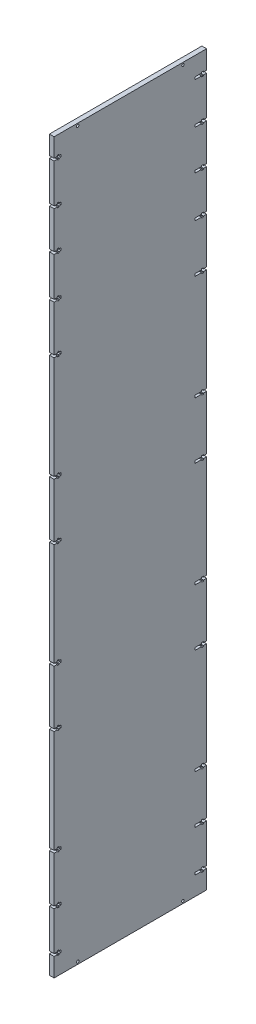
SolidWorks part; units mm, degrees
material "Acrylic (Medium-high impact)"
ref_plane "Front Plane" through (0, 0, 0) normal (0, 0, 1) x (1, 0, 0)
ref_plane "Top Plane" through (0, 0, 0) normal (0, 1, 0) x (1, 0, 0)
ref_plane "Right Plane" through (0, 0, 0) normal (1, 0, 0) x (0, 0, -1)
sketch "Sketch1" plane through (0, 0, 0) normal (1, 0, 0) x (0, 0, -1)
  line L0 (0, 100) -> (188.4, 100) construction
  line L1 (0, 0) -> (188.4, 0)
  line L2 (0, 0) -> (0, 900)
  line L3 (0, 900) -> (188.4, 900)
  line L4 (188.4, 0) -> (188.4, 900)
  line L5 (94.2, 900) -> (94.2, 0) construction
  line L6 (0, 450) -> (188.4, 450) construction
  line L7 (0, 300) -> (188.4, 300) construction
  line L8 (0, 500) -> (188.4, 500) construction
  line L9 (0, 700) -> (188.4, 700) construction
  line L10 (0, 800) -> (188.4, 800) construction
  line L11 (0, 850) -> (188.4, 850) construction
  line L12 (0, 750) -> (188.4, 750) construction
  line L13 (0, 600) -> (188.4, 600) construction
  line L14 (0, 400) -> (188.4, 400) construction
  line L15 (0, 200) -> (188.4, 200) construction
  line L16 (0, 50) -> (188.4, 50) construction
  line L29 (6.35, 877) -> (6.35, 878.21)
  line L30 (8.35, 874) -> (8.35, 877)
  line L31 (6.35, 877) -> (8.35, 877)
  line L32 (6.35, 874) -> (8.35, 874)
  line L33 (6.35, 872.79) -> (6.35, 874)
  line L34 (4, 878.21) -> (6.35, 878.21)
  line L35 (4, 872.79) -> (4, 874)
  line L36 (4, 872.79) -> (6.35, 872.79)
  line L37 (4, 877) -> (4, 878.21)
  line L38 (0, 877) -> (4, 877)
  line L39 (0, 874) -> (0, 877)
  line L40 (0, 874) -> (4, 874)
  line L41 (0, 826) -> (4, 826)
  line L42 (0, 826) -> (0, 823)
  line L43 (0, 823) -> (4, 823)
  line L44 (4, 823) -> (4, 821.79)
  line L45 (4, 827.21) -> (6.35, 827.21)
  line L46 (4, 827.21) -> (4, 826)
  line L47 (4, 821.79) -> (6.35, 821.79)
  line L48 (6.35, 827.21) -> (6.35, 826)
  line L49 (6.35, 826) -> (8.35, 826)
  line L50 (6.35, 823) -> (8.35, 823)
  line L51 (8.35, 826) -> (8.35, 823)
  line L52 (6.35, 823) -> (6.35, 821.79)
  line L53 (6.35, 777) -> (6.35, 778.21)
  line L54 (8.35, 774) -> (8.35, 777)
  line L55 (6.35, 777) -> (8.35, 777)
  line L56 (6.35, 774) -> (8.35, 774)
  line L57 (6.35, 772.79) -> (6.35, 774)
  line L58 (4, 778.21) -> (6.35, 778.21)
  line L59 (4, 772.79) -> (4, 774)
  line L60 (4, 772.79) -> (6.35, 772.79)
  line L61 (4, 777) -> (4, 778.21)
  line L62 (0, 777) -> (4, 777)
  line L63 (0, 774) -> (0, 777)
  line L64 (0, 774) -> (4, 774)
  line L65 (0, 726) -> (4, 726)
  line L66 (0, 726) -> (0, 723)
  line L67 (0, 723) -> (4, 723)
  line L68 (4, 723) -> (4, 721.79)
  line L69 (4, 727.21) -> (6.35, 727.21)
  line L70 (4, 727.21) -> (4, 726)
  line L71 (4, 721.79) -> (6.35, 721.79)
  line L72 (6.35, 727.21) -> (6.35, 726)
  line L73 (6.35, 726) -> (8.35, 726)
  line L74 (6.35, 723) -> (8.35, 723)
  line L75 (8.35, 726) -> (8.35, 723)
  line L76 (6.35, 723) -> (6.35, 721.79)
  line L77 (6.35, 666.5) -> (6.35, 667.71)
  line L78 (8.35, 663.5) -> (8.35, 666.5)
  line L79 (6.35, 666.5) -> (8.35, 666.5)
  line L80 (6.35, 663.5) -> (8.35, 663.5)
  line L81 (6.35, 662.29) -> (6.35, 663.5)
  line L82 (4, 667.71) -> (6.35, 667.71)
  line L83 (4, 662.29) -> (4, 663.5)
  line L84 (4, 662.29) -> (6.35, 662.29)
  line L85 (4, 666.5) -> (4, 667.71)
  line L86 (0, 666.5) -> (4, 666.5)
  line L87 (0, 663.5) -> (4, 663.5)
  line L88 (0, 666.5) -> (0, 663.5)
  line L89 (0, 533.5) -> (0, 536.5)
  line L90 (0, 536.5) -> (4, 536.5)
  line L91 (0, 533.5) -> (4, 533.5)
  line L92 (4, 533.5) -> (4, 532.29)
  line L93 (4, 537.71) -> (6.35, 537.71)
  line L94 (4, 537.71) -> (4, 536.5)
  line L95 (4, 532.29) -> (6.35, 532.29)
  line L96 (6.35, 537.71) -> (6.35, 536.5)
  line L97 (6.35, 536.5) -> (8.35, 536.5)
  line L98 (6.35, 533.5) -> (8.35, 533.5)
  line L99 (8.35, 536.5) -> (8.35, 533.5)
  line L100 (6.35, 533.5) -> (6.35, 532.29)
  line L101 (0, 336.5) -> (4, 336.5)
  line L102 (0, 333.5) -> (4, 333.5)
  line L103 (4, 333.5) -> (4, 332.29)
  line L104 (4, 337.71) -> (6.35, 337.71)
  line L105 (4, 337.71) -> (4, 336.5)
  line L106 (4, 332.29) -> (6.35, 332.29)
  line L107 (6.35, 337.71) -> (6.35, 336.5)
  line L108 (6.35, 336.5) -> (8.35, 336.5)
  line L109 (6.35, 333.5) -> (8.35, 333.5)
  line L110 (8.35, 336.5) -> (8.35, 333.5)
  line L111 (6.35, 333.5) -> (6.35, 332.29)
  line L112 (6.35, 466.5) -> (6.35, 467.71)
  line L113 (8.35, 463.5) -> (8.35, 466.5)
  line L114 (6.35, 466.5) -> (8.35, 466.5)
  line L115 (6.35, 463.5) -> (8.35, 463.5)
  line L116 (6.35, 462.29) -> (6.35, 463.5)
  line L117 (4, 467.71) -> (6.35, 467.71)
  line L118 (4, 462.29) -> (4, 463.5)
  line L119 (4, 462.29) -> (6.35, 462.29)
  line L120 (4, 466.5) -> (4, 467.71)
  line L121 (0, 466.5) -> (4, 466.5)
  line L122 (0, 463.5) -> (4, 463.5)
  line L123 (0, 136.5) -> (4, 136.5)
  line L124 (0, 133.5) -> (4, 133.5)
  line L125 (4, 133.5) -> (4, 132.29)
  line L126 (4, 137.71) -> (6.35, 137.71)
  line L127 (4, 137.71) -> (4, 136.5)
  line L128 (4, 132.29) -> (6.35, 132.29)
  line L129 (6.35, 137.71) -> (6.35, 136.5)
  line L130 (6.35, 136.5) -> (8.35, 136.5)
  line L131 (6.35, 133.5) -> (8.35, 133.5)
  line L132 (8.35, 136.5) -> (8.35, 133.5)
  line L133 (6.35, 133.5) -> (6.35, 132.29)
  line L134 (6.35, 266.5) -> (6.35, 267.71)
  line L135 (8.35, 263.5) -> (8.35, 266.5)
  line L136 (6.35, 266.5) -> (8.35, 266.5)
  line L137 (6.35, 263.5) -> (8.35, 263.5)
  line L138 (6.35, 262.29) -> (6.35, 263.5)
  line L139 (4, 267.71) -> (6.35, 267.71)
  line L140 (4, 262.29) -> (4, 263.5)
  line L141 (4, 262.29) -> (6.35, 262.29)
  line L142 (4, 266.5) -> (4, 267.71)
  line L143 (0, 266.5) -> (4, 266.5)
  line L144 (0, 263.5) -> (4, 263.5)
  line L145 (6.35, 77) -> (6.35, 78.21)
  line L146 (8.35, 74) -> (8.35, 77)
  line L147 (6.35, 77) -> (8.35, 77)
  line L148 (6.35, 74) -> (8.35, 74)
  line L149 (6.35, 72.79) -> (6.35, 74)
  line L150 (4, 78.21) -> (6.35, 78.21)
  line L151 (4, 72.79) -> (4, 74)
  line L152 (4, 72.79) -> (6.35, 72.79)
  line L153 (4, 77) -> (4, 78.21)
  line L154 (0, 77) -> (4, 77)
  line L155 (0, 74) -> (4, 74)
  line L156 (0, 26) -> (4, 26)
  line L157 (0, 23) -> (4, 23)
  line L158 (4, 23) -> (4, 21.79)
  line L159 (4, 27.21) -> (6.35, 27.21)
  line L160 (4, 27.21) -> (4, 26)
  line L161 (4, 21.79) -> (6.35, 21.79)
  line L162 (6.35, 27.21) -> (6.35, 26)
  line L163 (6.35, 26) -> (8.35, 26)
  line L164 (6.35, 23) -> (8.35, 23)
  line L165 (8.35, 26) -> (8.35, 23)
  line L166 (6.35, 23) -> (6.35, 21.79)
  line L167 (0, 74) -> (0, 24.2711) construction
  line L168 (188.4, 23) -> (184.4, 23)
  line L169 (188.4, 26) -> (184.4, 26)
  line L170 (182.05, 23) -> (182.05, 21.79)
  line L171 (180.05, 26) -> (180.05, 23)
  line L172 (182.05, 23) -> (180.05, 23)
  line L173 (182.05, 26) -> (180.05, 26)
  line L174 (182.05, 27.21) -> (182.05, 26)
  line L175 (184.4, 21.79) -> (182.05, 21.79)
  line L176 (184.4, 27.21) -> (184.4, 26)
  line L177 (184.4, 27.21) -> (182.05, 27.21)
  line L178 (184.4, 23) -> (184.4, 21.79)
  line L179 (188.4, 74) -> (184.4, 74)
  line L180 (188.4, 77) -> (184.4, 77)
  line L181 (184.4, 77) -> (184.4, 78.21)
  line L182 (184.4, 72.79) -> (182.05, 72.79)
  line L183 (184.4, 72.79) -> (184.4, 74)
  line L184 (184.4, 78.21) -> (182.05, 78.21)
  line L185 (182.05, 72.79) -> (182.05, 74)
  line L186 (182.05, 74) -> (180.05, 74)
  line L187 (182.05, 77) -> (180.05, 77)
  line L188 (180.05, 74) -> (180.05, 77)
  line L189 (182.05, 77) -> (182.05, 78.21)
  line L190 (182.05, 133.5) -> (182.05, 132.29)
  line L191 (180.05, 136.5) -> (180.05, 133.5)
  line L192 (182.05, 133.5) -> (180.05, 133.5)
  line L193 (182.05, 136.5) -> (180.05, 136.5)
  line L194 (182.05, 137.71) -> (182.05, 136.5)
  line L195 (184.4, 132.29) -> (182.05, 132.29)
  line L196 (184.4, 137.71) -> (184.4, 136.5)
  line L197 (184.4, 137.71) -> (182.05, 137.71)
  line L198 (184.4, 133.5) -> (184.4, 132.29)
  line L199 (188.4, 133.5) -> (184.4, 133.5)
  line L200 (188.4, 136.5) -> (184.4, 136.5)
  line L201 (188.4, 263.5) -> (184.4, 263.5)
  line L202 (188.4, 266.5) -> (184.4, 266.5)
  line L203 (184.4, 266.5) -> (184.4, 267.71)
  line L204 (184.4, 262.29) -> (182.05, 262.29)
  line L205 (184.4, 262.29) -> (184.4, 263.5)
  line L206 (184.4, 267.71) -> (182.05, 267.71)
  line L207 (182.05, 262.29) -> (182.05, 263.5)
  line L208 (182.05, 263.5) -> (180.05, 263.5)
  line L209 (182.05, 266.5) -> (180.05, 266.5)
  line L210 (180.05, 263.5) -> (180.05, 266.5)
  line L211 (182.05, 266.5) -> (182.05, 267.71)
  line L212 (182.05, 333.5) -> (182.05, 332.29)
  line L213 (180.05, 336.5) -> (180.05, 333.5)
  line L214 (182.05, 333.5) -> (180.05, 333.5)
  line L215 (182.05, 336.5) -> (180.05, 336.5)
  line L216 (182.05, 337.71) -> (182.05, 336.5)
  line L217 (184.4, 332.29) -> (182.05, 332.29)
  line L218 (184.4, 337.71) -> (184.4, 336.5)
  line L219 (184.4, 337.71) -> (182.05, 337.71)
  line L220 (184.4, 333.5) -> (184.4, 332.29)
  line L221 (188.4, 333.5) -> (184.4, 333.5)
  line L222 (188.4, 336.5) -> (184.4, 336.5)
  line L223 (188.4, 463.5) -> (184.4, 463.5)
  line L224 (188.4, 466.5) -> (184.4, 466.5)
  line L225 (184.4, 466.5) -> (184.4, 467.71)
  line L226 (184.4, 462.29) -> (182.05, 462.29)
  line L227 (184.4, 462.29) -> (184.4, 463.5)
  line L228 (184.4, 467.71) -> (182.05, 467.71)
  line L229 (182.05, 462.29) -> (182.05, 463.5)
  line L230 (182.05, 463.5) -> (180.05, 463.5)
  line L231 (182.05, 466.5) -> (180.05, 466.5)
  line L232 (180.05, 463.5) -> (180.05, 466.5)
  line L233 (182.05, 466.5) -> (182.05, 467.71)
  line L234 (182.05, 533.5) -> (182.05, 532.29)
  line L235 (180.05, 536.5) -> (180.05, 533.5)
  line L236 (182.05, 533.5) -> (180.05, 533.5)
  line L237 (182.05, 536.5) -> (180.05, 536.5)
  line L238 (182.05, 537.71) -> (182.05, 536.5)
  line L239 (184.4, 532.29) -> (182.05, 532.29)
  line L240 (184.4, 537.71) -> (184.4, 536.5)
  line L241 (184.4, 537.71) -> (182.05, 537.71)
  line L242 (184.4, 533.5) -> (184.4, 532.29)
  line L243 (188.4, 533.5) -> (184.4, 533.5)
  line L244 (188.4, 536.5) -> (184.4, 536.5)
  line L245 (188.4, 663.5) -> (184.4, 663.5)
  line L246 (188.4, 666.5) -> (184.4, 666.5)
  line L247 (184.4, 666.5) -> (184.4, 667.71)
  line L248 (184.4, 662.29) -> (182.05, 662.29)
  line L249 (184.4, 662.29) -> (184.4, 663.5)
  line L250 (184.4, 667.71) -> (182.05, 667.71)
  line L251 (182.05, 662.29) -> (182.05, 663.5)
  line L252 (182.05, 663.5) -> (180.05, 663.5)
  line L253 (182.05, 666.5) -> (180.05, 666.5)
  line L254 (180.05, 663.5) -> (180.05, 666.5)
  line L255 (182.05, 666.5) -> (182.05, 667.71)
  line L256 (182.05, 723) -> (182.05, 721.79)
  line L257 (180.05, 726) -> (180.05, 723)
  line L258 (182.05, 723) -> (180.05, 723)
  line L259 (182.05, 726) -> (180.05, 726)
  line L260 (182.05, 727.21) -> (182.05, 726)
  line L261 (184.4, 721.79) -> (182.05, 721.79)
  line L262 (184.4, 727.21) -> (184.4, 726)
  line L263 (184.4, 727.21) -> (182.05, 727.21)
  line L264 (184.4, 723) -> (184.4, 721.79)
  line L265 (188.4, 723) -> (184.4, 723)
  line L266 (188.4, 726) -> (184.4, 726)
  line L267 (188.4, 774) -> (184.4, 774)
  line L268 (188.4, 777) -> (184.4, 777)
  line L269 (184.4, 777) -> (184.4, 778.21)
  line L270 (184.4, 772.79) -> (182.05, 772.79)
  line L271 (184.4, 772.79) -> (184.4, 774)
  line L272 (184.4, 778.21) -> (182.05, 778.21)
  line L273 (182.05, 772.79) -> (182.05, 774)
  line L274 (182.05, 774) -> (180.05, 774)
  line L275 (182.05, 777) -> (180.05, 777)
  line L276 (180.05, 774) -> (180.05, 777)
  line L277 (182.05, 777) -> (182.05, 778.21)
  line L278 (182.05, 823) -> (182.05, 821.79)
  line L279 (180.05, 826) -> (180.05, 823)
  line L280 (182.05, 823) -> (180.05, 823)
  line L281 (182.05, 826) -> (180.05, 826)
  line L282 (182.05, 827.21) -> (182.05, 826)
  line L283 (184.4, 821.79) -> (182.05, 821.79)
  line L284 (184.4, 827.21) -> (184.4, 826)
  line L285 (184.4, 827.21) -> (182.05, 827.21)
  line L286 (184.4, 823) -> (184.4, 821.79)
  line L287 (188.4, 823) -> (184.4, 823)
  line L288 (188.4, 826) -> (184.4, 826)
  line L289 (188.4, 874) -> (184.4, 874)
  line L290 (188.4, 877) -> (184.4, 877)
  line L291 (184.4, 877) -> (184.4, 878.21)
  line L292 (184.4, 872.79) -> (182.05, 872.79)
  line L293 (184.4, 872.79) -> (184.4, 874)
  line L294 (184.4, 878.21) -> (182.05, 878.21)
  line L295 (182.05, 872.79) -> (182.05, 874)
  line L296 (182.05, 874) -> (180.05, 874)
  line L297 (182.05, 877) -> (180.05, 877)
  line L298 (180.05, 874) -> (180.05, 877)
  line L299 (182.05, 877) -> (182.05, 878.21)
  line L301 (12.141, 850) -> (0, 850) construction
  line L317 (12.141, 750) -> (0, 750) construction
  line L323 (12.141, 600) -> (0, 600) construction
  line L329 (12.141, 50) -> (0, 50) construction
  line L335 (12.141, 200) -> (0, 200) construction
  line L341 (12.141, 400) -> (0, 400) construction
  point P38 (8.35, 75.5)
  point P51 (8.35, 875.5)
  point P102 (8.35, 665)
  point P120 (94.2, 450)
  dimension "D1" = 900
  dimension "D2" = 188.4
  dimension "D3" = 100
  dimension "D4" = 100
  dimension "D5" = 200
  dimension "D6" = 200
  dimension "D7" = 200
  dimension "D8" = 50
  dimension "D9" = 100
  dimension "D10" = 100
  dimension "D11" = 100
  dimension "D12" = 50
  dimension "D13" = 50
  dimension "D14" = 4
  dimension "D15" = 2.35
  dimension "D16" = 2
  dimension "D17" = 4
  dimension "D18" = 2.35
  dimension "D19" = 2
  dimension "D20" = 5.42
  dimension "D21" = 3
  dimension "D22" = 25.5
  dimension "D23" = 65
  dimension "D24" = 3
  dimension "D25" = 5.42
  dimension "D26" = 3
  dimension "D27" = 25.5
extrude "Boss-Extrude1" add sketch "Sketch1" along normal blind 5.8 contours L297 L299 L294 L291 L290 L4 L3 L2 L38 L37 L34 L29 L31 L30 L32 L33 L36 L35 L40 L41 L46 L45 L48 L49 L51 L50 L52 L47 L44 L43 L62 L61 L58 L53 L55 L54 L56 L57 L60 L59 L64 L65 L70 L69 L72 L73 L75 L74
sketch "Sketch2" plane through (5.8, 0, 0) normal (1, 0, 0) x (0, 0, -1)
  line L0 (94.2, 900) -> (94.2, 0) construction
  line L1 (0, 900) -> (188.4, 900) construction
  line L2 (0, 0) -> (188.4, 0) construction
  line L3 (94.2, 450) -> (188.4, 450) construction
  line L4 (188.4, 336.5) -> (188.4, 463.5) construction
  circle A0 centre (159.2, 897.1) radius 1.55
  circle A1 centre (29.2, 897.1) radius 1.55
  circle A2 centre (159.2, 2.9) radius 1.55
  circle A3 centre (29.2, 2.9) radius 1.55
  dimension "D2" = 3.1
  dimension "D1" = 65
  dimension "D3" = 2.9
extrude "Cut-Extrude1" cut sketch "Sketch2" against normal up to surface (5.8 mm away) up to face at (0, 474.6575, -94.2)
sketch "Sketch3" plane through (5.8, 0, 0) normal (1, 0, 0) x (0, 0, -1)
  line L0 (182.05, 874) -> (180.05, 874) construction
  line L1 (180.05, 877) -> (174.05, 877)
  line L2 (180.05, 877) -> (180.05, 874)
  line L3 (180.05, 874) -> (174.05, 874)
  line L4 (174.05, 877) -> (174.05, 874)
  line L5 (177.05, 874) -> (177.05, 877) construction
  line L6 (180.05, 875.5) -> (174.05, 875.5) construction
  line L7 (180.05, 823) -> (174.05, 823)
  line L8 (180.05, 826) -> (174.05, 826)
  line L9 (174.05, 826) -> (174.05, 823)
  line L10 (180.05, 826) -> (180.05, 823)
  line L11 (188.4, 800) -> (171.8921, 800) construction
  line L12 (188.4, 777) -> (188.4, 823) construction
  line L13 (180.05, 724.5) -> (174.05, 724.5) construction
  line L14 (177.05, 726) -> (177.05, 723) construction
  line L15 (180.05, 774) -> (180.05, 777)
  line L16 (174.05, 774) -> (174.05, 777)
  line L17 (180.05, 774) -> (174.05, 774)
  line L18 (180.05, 777) -> (174.05, 777)
  line L19 (174.05, 723) -> (174.05, 726)
  line L20 (180.05, 726) -> (174.05, 726)
  line L21 (180.05, 723) -> (180.05, 726)
  line L22 (180.05, 723) -> (174.05, 723)
  line L23 (182.05, 663.5) -> (180.05, 663.5) construction
  line L24 (180.05, 666.5) -> (174.05, 666.5)
  line L25 (180.05, 666.5) -> (180.05, 663.5)
  line L26 (180.05, 663.5) -> (174.05, 663.5)
  line L27 (174.05, 666.5) -> (174.05, 663.5)
  line L28 (177.05, 663.5) -> (177.05, 666.5) construction
  line L29 (180.05, 665) -> (174.05, 665) construction
  line L30 (180.05, 536.5) -> (174.05, 536.5)
  line L31 (180.05, 536.5) -> (180.05, 533.5)
  line L32 (180.05, 533.5) -> (174.05, 533.5)
  line L33 (174.05, 536.5) -> (174.05, 533.5)
  line L34 (177.05, 533.5) -> (177.05, 536.5) construction
  line L35 (180.05, 535) -> (174.05, 535) construction
  line L36 (188.4, 500) -> (155.0875, 500) construction
  line L37 (188.4, 466.5) -> (188.4, 533.5) construction
  line L38 (180.05, 465) -> (174.05, 465) construction
  line L39 (177.05, 466.5) -> (177.05, 463.5) construction
  line L40 (180.05, 335) -> (174.05, 335) construction
  line L41 (177.05, 336.5) -> (177.05, 333.5) construction
  line L42 (174.05, 463.5) -> (174.05, 466.5)
  line L43 (180.05, 466.5) -> (174.05, 466.5)
  line L44 (180.05, 463.5) -> (180.05, 466.5)
  line L45 (180.05, 463.5) -> (174.05, 463.5)
  line L46 (174.05, 333.5) -> (174.05, 336.5)
  line L47 (180.05, 336.5) -> (174.05, 336.5)
  line L48 (180.05, 333.5) -> (180.05, 336.5)
  line L49 (180.05, 333.5) -> (174.05, 333.5)
  line L50 (188.4, 300) -> (155.0875, 300) construction
  line L51 (188.4, 266.5) -> (188.4, 333.5) construction
  line L52 (177.05, 263.5) -> (177.05, 266.5) construction
  line L53 (180.05, 265) -> (174.05, 265) construction
  line L54 (177.05, 133.5) -> (177.05, 136.5) construction
  line L55 (180.05, 135) -> (174.05, 135) construction
  line L56 (180.05, 266.5) -> (174.05, 266.5)
  line L57 (180.05, 266.5) -> (180.05, 263.5)
  line L58 (180.05, 263.5) -> (174.05, 263.5)
  line L59 (174.05, 266.5) -> (174.05, 263.5)
  line L60 (180.05, 136.5) -> (174.05, 136.5)
  line L61 (180.05, 136.5) -> (180.05, 133.5)
  line L62 (180.05, 133.5) -> (174.05, 133.5)
  line L63 (174.05, 136.5) -> (174.05, 133.5)
  line L64 (182.05, 74) -> (180.05, 74) construction
  line L65 (180.05, 77) -> (174.05, 77)
  line L66 (180.05, 77) -> (180.05, 74)
  line L67 (180.05, 74) -> (174.05, 74)
  line L68 (174.05, 77) -> (174.05, 74)
  line L69 (177.05, 74) -> (177.05, 77) construction
  line L70 (180.05, 75.5) -> (174.05, 75.5) construction
  line L71 (180.05, 26) -> (174.05, 26)
  line L72 (180.05, 26) -> (180.05, 23)
  line L73 (180.05, 23) -> (174.05, 23)
  line L74 (174.05, 26) -> (174.05, 23)
  line L75 (177.05, 23) -> (177.05, 26) construction
  line L76 (180.05, 24.5) -> (174.05, 24.5) construction
  point P26 (177.05, 724.5)
  point P43 (177.05, 535)
  point P62 (177.05, 335)
  point P63 (177.05, 465)
  point P84 (177.05, 135)
  point P85 (177.05, 265)
  point P255 (177.05, 665)
  point P307 (177.05, 24.5)
  point P320 (177.05, 875.5)
  point P346 (177.05, 75.5)
  dimension "D1" = 6
  dimension "D2" = 2
  dimension "D3" = 2
extrude "Cut-Extrude2" cut sketch "Sketch3" against normal up to surface (5.8 mm away) up to face at (0, 897.1, -30.75)
